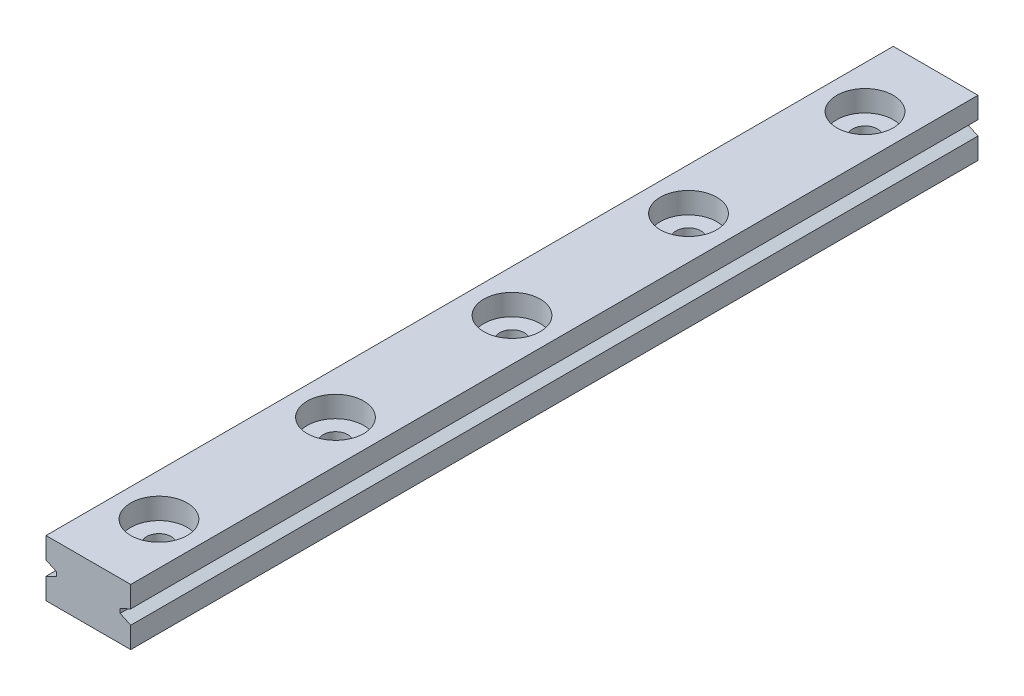
SolidWorks part; units mm, degrees
material "合金钢"
ref_plane "前视基准面" through (0, 0, 0) normal (0, 0, 1) x (1, 0, 0)
ref_plane "上视基准面" through (0, 0, 0) normal (0, 1, 0) x (1, 0, 0)
ref_plane "右视基准面" through (0, 0, 0) normal (1, 0, 0) x (0, 0, -1)
sketch "草图1" plane through (0, 0, 0) normal (0, 0, 1) x (1, 0, 0)
  line L1 (-6, 4) -> (6, 4)
  line L2 (-6, 4) -> (-6, -4)
  line L3 (-6, -4) -> (6, -4)
  line L4 (6, 4) -> (6, -4)
  line L5 (-6, 4) -> (6, -4) construction
  line L6 (-6, -4) -> (6, 4) construction
  point P0 (0, 0)
  dimension "D1" = 8
  dimension "D2" = 12
extrude "凸台-拉伸1" add sketch "草图1" along normal blind 120
sketch "草图2" plane through (0, 4, 0) normal (0, 1, 0) x (1, 0, 0)
  line L0 (0, 0) -> (0, -84.8716) construction
  line L1 (6, 0) -> (-6, 0) construction
  circle A0 centre (0, -10) radius 1.75
  circle A1 centre (0, -35) radius 1.75
  circle A2 centre (0, -60) radius 1.75
  circle A3 centre (0, -85) radius 1.75
  circle A4 centre (0, -110) radius 1.75
  circle A5 centre (0, -135) radius 1.75
  circle A6 centre (0, -160) radius 1.75
  circle A7 centre (0, -185) radius 1.75
  circle A8 centre (0, -210) radius 1.75
  circle A9 centre (0, -235) radius 1.75
  circle A10 centre (0, -260) radius 1.75
  circle A11 centre (0, -285) radius 1.75
  dimension "D1" = 3.5
  dimension "D2" = 10
  dimension "D4" = 25
  dimension "D3" = 12
extrude "切除-拉伸1" cut sketch "草图2" against normal through all
sketch "草图3" plane through (0, 4, 0) normal (0, 1, 0) x (1, 0, 0)
  circle A0 centre (0, -10) radius 4
  circle A1 centre (0, -35) radius 4
  circle A2 centre (0, -60) radius 4
  circle A3 centre (0, -85) radius 4
  circle A4 centre (0, -110) radius 4
  circle A5 centre (0, -135) radius 4
  circle A6 centre (0, -160) radius 4
  circle A7 centre (0, -185) radius 4
  circle A8 centre (0, -210) radius 4
  circle A9 centre (0, -235) radius 4
  circle A10 centre (0, -260) radius 4
  circle A11 centre (0, -285) radius 4
  dimension "D1" = 8
  dimension "D3" = 25
  dimension "D2" = 12
extrude "切除-拉伸2" cut sketch "草图3" against normal blind 3
sketch "草图4" plane through (0, 0, 0) normal (0, 0, -1) x (-1, 0, 0)
  line L0 (0, 4) -> (0, -4) construction
  line L1 (-6, 4) -> (6, 4) construction
  line L2 (6, -4) -> (-6, -4) construction
  line L3 (6, 1) -> (4.5, 0.3)
  line L4 (6, 4) -> (6, -4) construction
  line L5 (4.5, 0.3) -> (4.5, -0.3)
  line L6 (4.5, -0.3) -> (6, -1)
  line L7 (4.5, 0) -> (8.1318, 0) construction
  line L8 (6, 1) -> (6, -1)
  line L9 (-6, 1) -> (-4.5, 0.3)
  line L10 (-4.5, 0.3) -> (-4.5, -0.3)
  line L11 (-4.5, -0.3) -> (-6, -1)
  line L12 (-6, 1) -> (-6, -1)
  dimension "D1" = 1.5
  dimension "D2" = 2
  dimension "D3" = 0.6
  dimension "D4" = 4
extrude "切除-拉伸3" cut sketch "草图4" against normal through all
